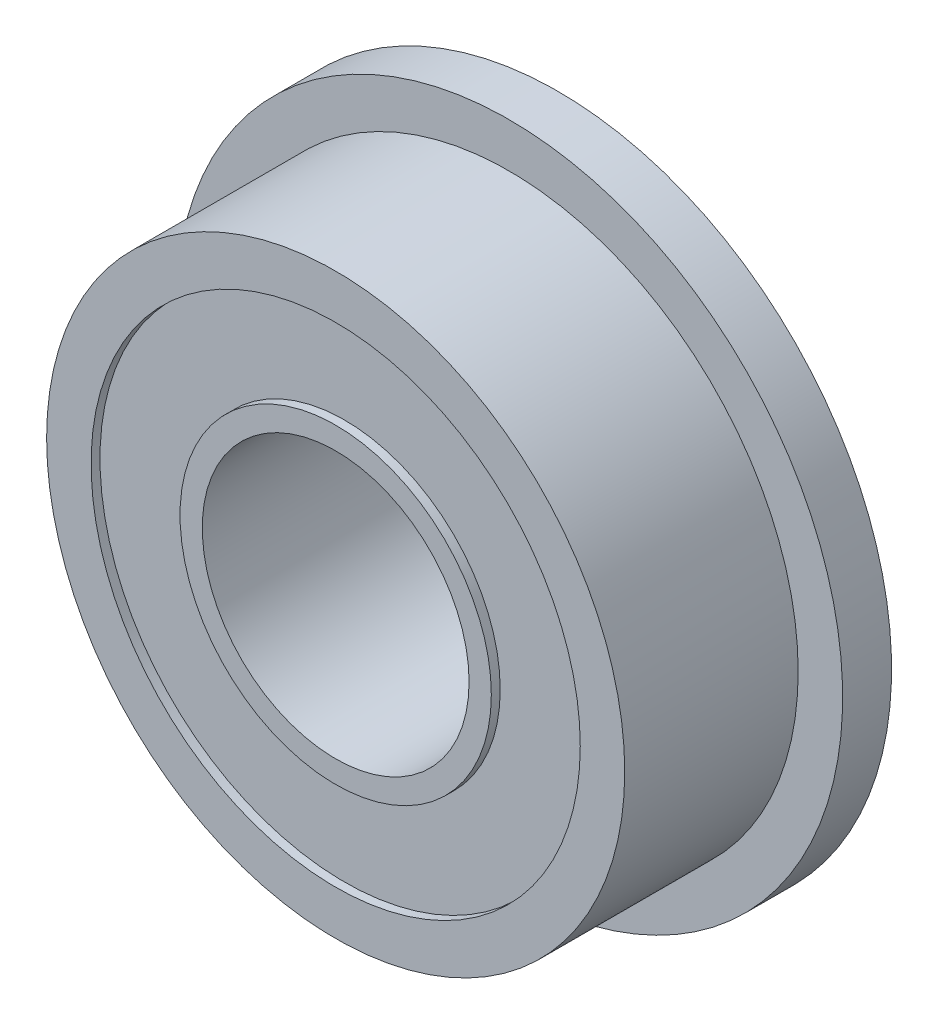
SolidWorks part; units mm, degrees
material "鉻不鏽鋼"
ref_plane "前基準面" through (0, 0, 0) normal (0, 0, 1) x (1, 0, 0)
ref_plane "上基準面" through (0, 0, 0) normal (0, 1, 0) x (1, 0, 0)
ref_plane "右基準面" through (0, 0, 0) normal (1, 0, 0) x (0, 0, -1)
sketch "草圖1" plane through (0, 0, 0) normal (0, 0, 1) x (1, 0, 0)
  circle A0 centre (0, 0) radius 6.5
  dimension "D1" = 13
extrude "填料-伸長1" add sketch "草圖1" along normal mid plane 5
sketch "草圖4" plane through (0, 0, -2.5) normal (0, 0, -1) x (-1, 0, 0)
  circle A0 centre (0, 0) radius 7.5
  dimension "D1" = 15
extrude "填料-伸長2" add sketch "草圖4" against normal blind 1.1
sketch "草圖2" plane through (0, 0, 2.5) normal (0, 0, 1) x (1, 0, 0)
  circle A0 centre (0, 0) radius 3
  dimension "D1" = 6
extrude "除料-伸長1" cut sketch "草圖2" against normal through all
sketch "草圖3" plane through (0, 0, 2.5) normal (0, 0, 1) x (1, 0, 0)
  circle A0 centre (0, 0) radius 5.5
  circle A1 centre (0, 0) radius 3.5
  dimension "D1" = 7
  dimension "D2" = 11
extrude "除料-伸長2" cut sketch "草圖3" against normal blind 0.2
mirror "鏡射1" about plane through (0, 0, 0) normal (0, 0, 1) of "除料-伸長2"
